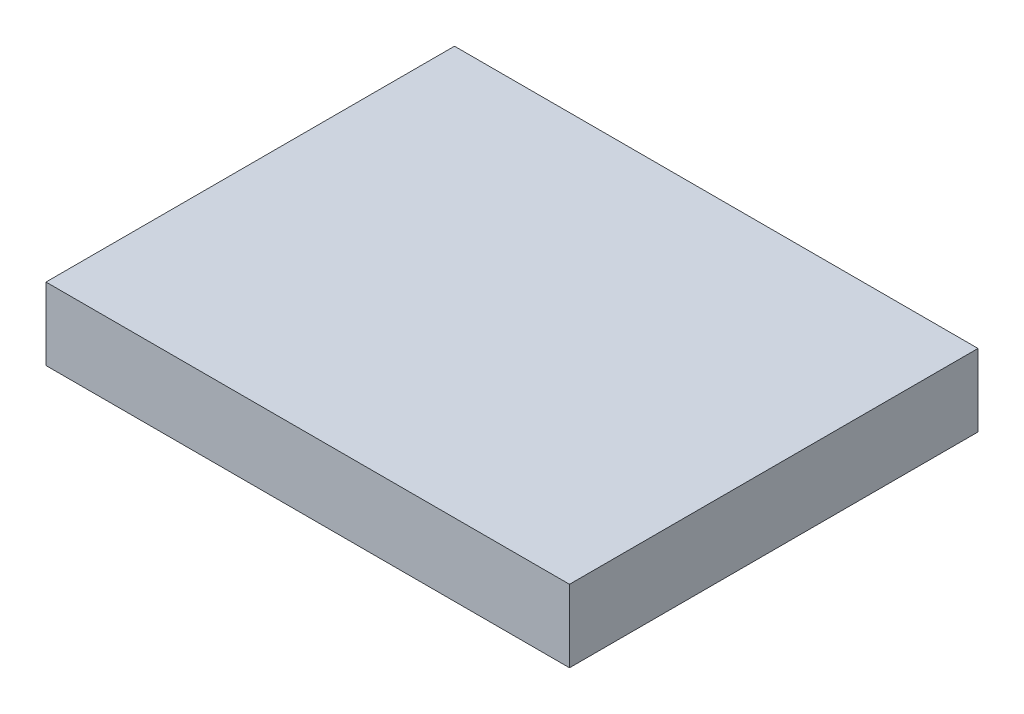
SolidWorks part; units mm, degrees
ref_plane "Płaszczyzna XY" through (0, 0, 0) normal (0, 0, 1) x (1, 0, 0)
ref_plane "Płaszczyzna XZ" through (0, 0, 0) normal (0, 1, 0) x (1, 0, 0)
ref_plane "Płaszczyzna YZ" through (0, 0, 0) normal (1, 0, 0) x (0, 0, -1)
sketch "Sketch1" plane through (-251.6452, 0, 0) normal (-1, 0, 0) x (0, 0, 1)
  line L0 (-448.7798, -100.1209) -> (-417.5675, -100.1209)
  line L1 (-448.7798, -100.1209) -> (-448.7798, -105.6488)
  line L2 (-417.5675, -100.1209) -> (-417.5675, -105.6488)
  line L3 (-448.7798, -105.6488) -> (-417.5675, -105.6488)
  dimension "D1" = 417.5675
  dimension "D2" = 448.7798
  dimension "D3" = 100.1209
  dimension "D4" = 105.6488
extrude "Boss-Extrude1" add sketch "Sketch1" along normal blind 40
